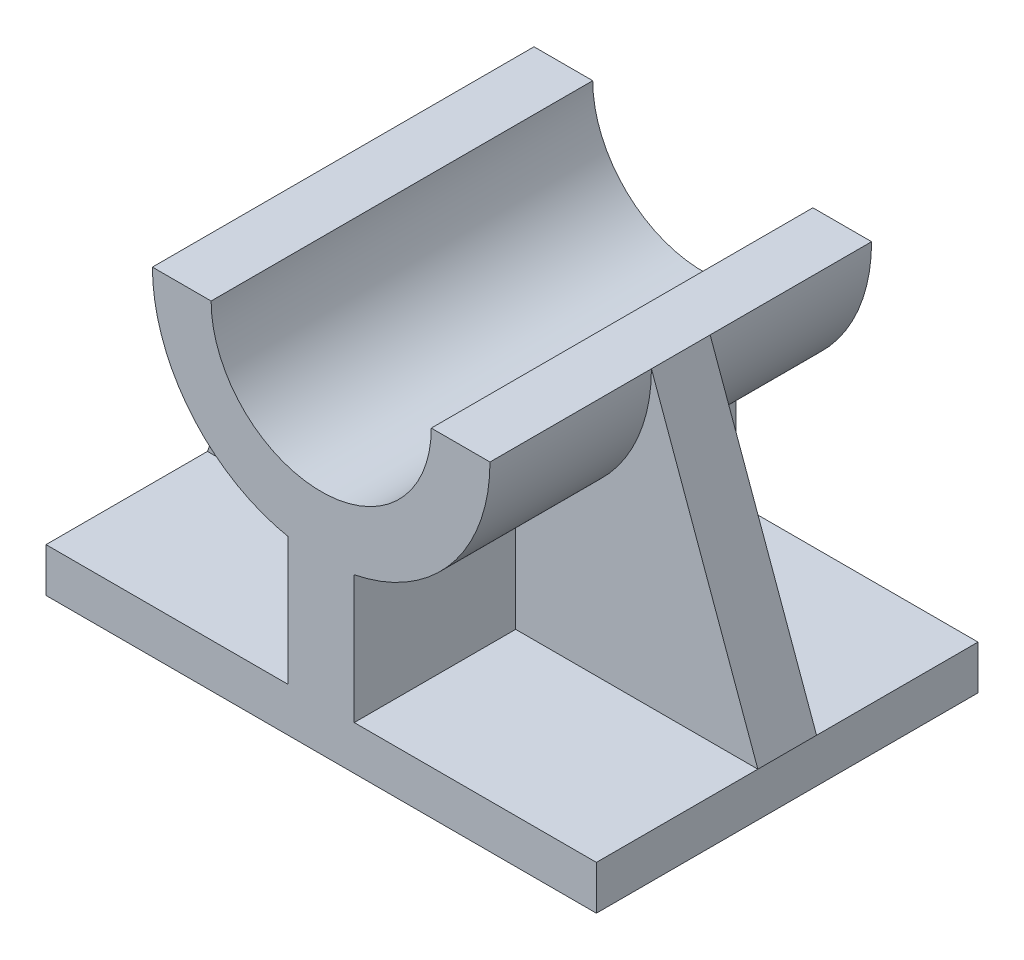
SolidWorks part; units mm, degrees
ref_plane "Front Plane" through (0, 0, 0) normal (0, 0, 1) x (1, 0, 0)
ref_plane "Top Plane" through (0, 0, 0) normal (0, 1, 0) x (1, 0, 0)
ref_plane "Right Plane" through (0, 0, 0) normal (1, 0, 0) x (0, 0, -1)
sketch "Sketch1" plane through (0, 0, 0) normal (0, 1, 0) x (1, 0, 0)
  line L1 (-37.5, 26) -> (37.5, 26)
  line L2 (-37.5, 26) -> (-37.5, -26)
  line L3 (-37.5, -26) -> (37.5, -26)
  line L4 (37.5, 26) -> (37.5, -26)
  line L5 (-37.5, 26) -> (37.5, -26) construction
  line L6 (-37.5, -26) -> (37.5, 26) construction
  point P0 (0, 0)
  dimension "D1" = 52
  dimension "D2" = 75
extrude "Boss-Extrude1" add sketch "Sketch1" along normal blind 6
sketch "Sketch2" plane through (0, 6, 0) normal (0, 1, 0) x (1, 0, 0)
  line L0 (0, 26) -> (0, -26) construction
  line L1 (37.5, 26) -> (-37.5, 26) construction
  line L2 (-37.5, -26) -> (37.5, -26) construction
  line L4 (-4.5, 26) -> (4.5, 26)
  line L5 (-4.5, 26) -> (-4.5, -26)
  line L6 (-4.5, -26) -> (4.5, -26)
  line L7 (4.5, 26) -> (4.5, -26)
  dimension "D1" = 9
  dimension "4.5" = 4.5
extrude "Boss-Extrude2" add sketch "Sketch2" along normal blind 17
sketch "Sketch3" plane through (0, 0, 26) normal (0, 0, 1) x (1, 0, 0)
  line L0 (0, 42.5347) -> (0, 0) construction
  line L1 (-4.5, 23) -> (4.5, 23) construction
  line L2 (-23, 46) -> (-15, 46)
  line L3 (15, 46) -> (23, 46)
  arc A0 (-23, 46) -> (23, 46) centre (0, 46) ccw
  arc A1 (-15, 46) -> (15, 46) centre (0, 46) ccw
  point P7 (0, 21.2673)
  dimension "D1" = 30
  dimension "D2" = 46
extrude "Boss-Extrude3" add sketch "Sketch3" against normal blind 52 separate body
sketch "Sketch6" plane through (0, 23, 0) normal (0, 1, 0) x (1, 0, 0)
  line L4 (-4.5, 26) -> (-4.5, -26)
  line L5 (-4.5, -26) -> (4.5, -26)
  line L6 (4.5, -26) -> (4.5, 26)
  line L7 (4.5, 26) -> (-4.5, 26)
  line L8 (-4.5, 26) -> (-4.5, -26)
  line L9 (-4.5, -26) -> (4.5, -26)
  line L10 (4.5, -26) -> (4.5, 26)
  line L11 (4.5, 26) -> (-4.5, 26)
  dimension "D1" = 0
extrude "Boss-Extrude5" add sketch "Sketch6" along normal up to surface (0.4445 mm away)
sketch "Sketch7" plane through (0, 0, 0) normal (0, 0, 1) x (1, 0, 0)
  line L0 (23, 46) -> (37.5, 6)
rib "Rib1" sketch "Sketch7" sketch "Sketch7" thickness 8 extrusion direction parallel to sketch draft on no parameters "D1"=8
mirror "Mirror3" about plane through (0, 0, 0) normal (1, 0, 0) of "Rib1"
